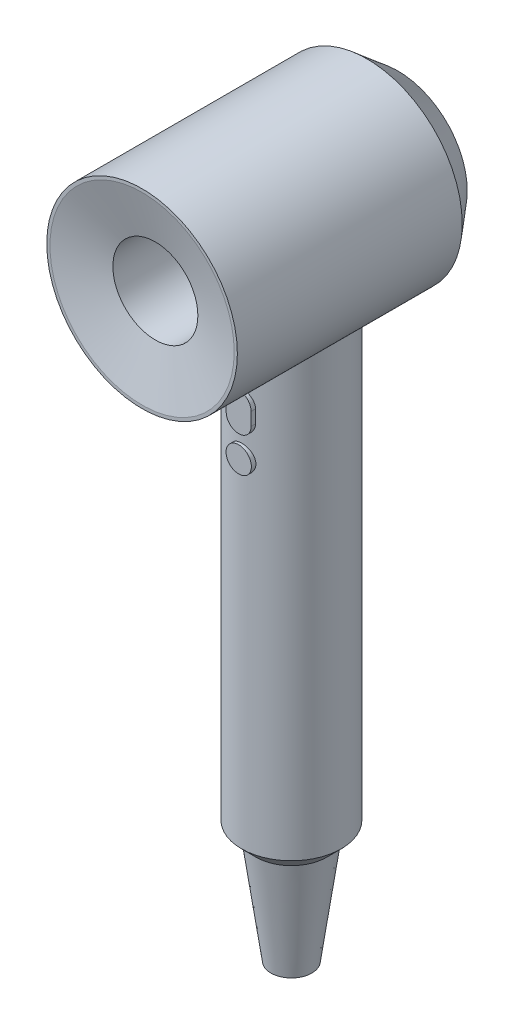
SolidWorks part; units mm, degrees
ref_plane "Front Plane" through (0, 0, 0) normal (0, 0, 1) x (1, 0, 0)
ref_plane "Top Plane" through (0, 0, 0) normal (0, 1, 0) x (1, 0, 0)
ref_plane "Right Plane" through (0, 0, 0) normal (1, 0, 0) x (0, 0, -1)
sketch "Sketch1" plane through (0, 0, 0) normal (0, 0, 1) x (1, 0, 0)
  line L0 (0, 0) -> (0, 288) construction
  line L1 (-38.5, 288) -> (38.5, 288) construction
  line L2 (-85.9301, 248.2745) -> (85.9301, 248.2745) construction
  line L3 (-11.5472, 336.0641) -> (156.4528, 336.0641) construction
  point P7 (0, 288)
  dimension "D1" = 288
  dimension "D2" = 77
sketch "Sketch2" plane through (0, 0, 0) normal (0, 0, 1) x (1, 0, 0)
  line L0 (-85.9301, 248.2745) -> (85.9301, 248.2745) construction
  line L1 (0, 0) -> (0, 288) construction
  line L2 (-19.1326, 213.9341) -> (-19.1326, 47.726)
  line L3 (18.8024, 47.726) -> (18.8024, 213.7523)
  line L4 (-19.1326, 87.2327) -> (18.8024, 87.2327)
  line L5 (-19.1326, 47.726) -> (18.8024, 47.726)
  line L6 (-19.1326, 47.726) -> (-14.161, 42.7544)
  line L7 (-14.161, 42.7544) -> (14.183, 42.7544)
  line L8 (14.183, 42.7544) -> (18.8024, 47.726)
  line L9 (-13.512, 42.7544) -> (-7.0098, 1.0508)
  line L10 (-7.0098, 1.0508) -> (6.9597, 1.0508)
  line L11 (6.9597, 1.0508) -> (13.5568, 42.7544)
  circle A0 centre (0, 248.2745) radius 16.2697
  circle A1 centre (0, 248.2745) radius 36.4827
  circle A2 centre (0, 248.2745) radius 39.3105
  circle A3 centre (11.6651, 223.5671) radius 2.936
  circle A4 centre (-11.9222, 223.5671) radius 3.0135
  circle A5 centre (0, 177.1026) radius 4.5669
  circle A6 centre (0, 177.1026) radius 5.3557
  circle A7 centre (0, 191.4798) radius 4.2295
extrude "Boss-Extrude1" add sketch "Sketch2" along normal blind 98 contours A1 A4 A3 A0
sketch "Sketch4" plane through (0, 0, 0) normal (1, 0, 0) x (0, 0, -1)
  line L0 (-146.5807, 329.9179) -> (60.7526, 329.9179) construction
  line L1 (-59.9095, 217.7569) -> (-59.9095, 46.8202)
  line L2 (-59.9095, 46.8202) -> (-54.3706, 41.2812)
  line L3 (-54.3706, 41.2812) -> (-48.6615, 0)
  line L9 (-48.6615, 0) -> (-40.8313, 0)
  line L10 (-59.9095, 217.7569) -> (-40.8313, 217.7569)
  line L11 (-40.8313, 217.7569) -> (-40.8313, 0) construction
  line L12 (-40.8313, 0) -> (-40.8313, 217.7569)
revolve "Revolve1" add sketch "Sketch4" angle 360 about L11
ref_plane "Plane1" through (0, 0, 40) normal (0, 0, 1) x (1, 0, 0)
sketch "Sketch5" plane through (0, 0, 40) normal (0, 0, 1) x (1, 0, 0)
  line L0 (533.787, 680.6474) -> (741.1204, 680.6474) construction
  line L1 (-83.1728, 336.0824) -> (84.8272, 336.0824) construction
  line L2 (4.7381, 194.7438) -> (4.7381, 189.7785)
  line L3 (-4.7872, 189.7785) -> (-4.7872, 194.7438)
  circle A0 centre (0, 176.5038) radius 4.846
  arc A2 (4.7381, 189.7785) -> (-4.7872, 189.7785) centre (-0.0246, 189.7785) cw
  arc A3 (-4.7872, 194.7438) -> (4.7381, 194.7438) centre (-0.0246, 194.7438) cw
extrude "Boss-Extrude2" add sketch "Sketch5" along normal blind 21 separate body
chamfer "Chamfer1" distance 19 angle 15 1 edges at (16.2697, 248.2745, 98)
chamfer "Chamfer2" distance 10 angle 50 1 edges at (36.4827, 248.2745, 0)
